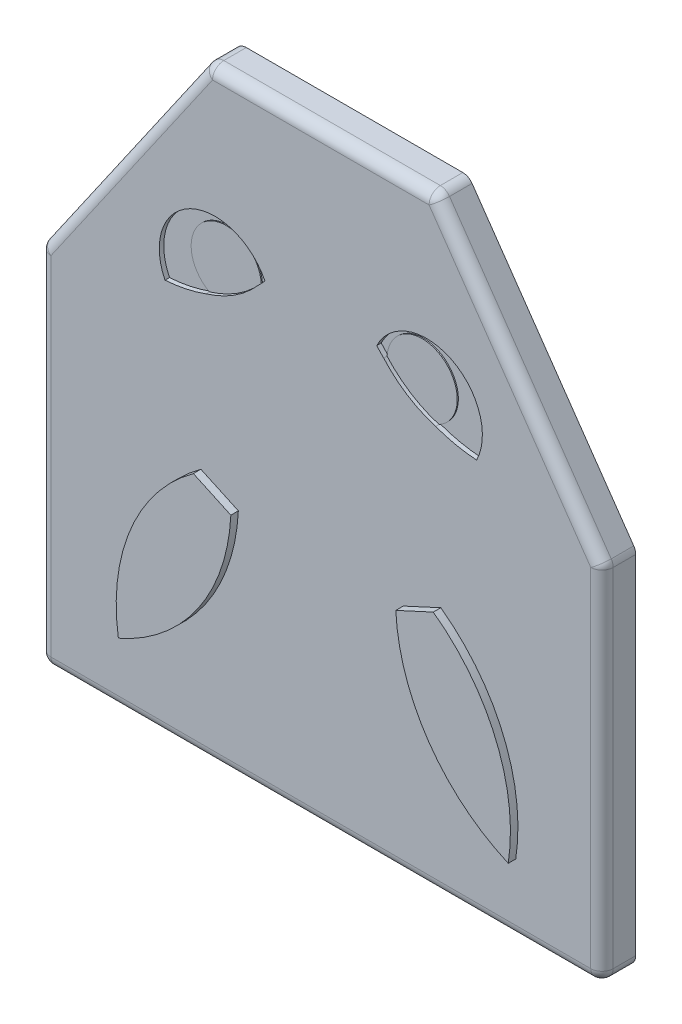
SolidWorks part; units mm, degrees
material "PS HI"
ref_plane "Face" through (0, 0, 0) normal (0, 0, 1) x (1, 0, 0)
ref_plane "Dessus" through (0, 0, 0) normal (0, 1, 0) x (1, 0, 0)
ref_plane "Droite" through (0, 0, 0) normal (1, 0, 0) x (0, 0, -1)
sketch "Esquisse1" plane through (0, 0, 0) normal (0, 0, 1) x (1, 0, 0)
  line L0 (0, 150.787) -> (0, -256.1207) construction
  line L1 (73, -52.6668) -> (-73, -52.6668)
  line L2 (-73, -52.6668) -> (-73, 41.3332)
  line L3 (-73, 41.3332) -> (-29.4, 104.1823)
  line L4 (-29.4, 104.1823) -> (29.4, 104.1823)
  line L5 (73, -52.6668) -> (73, 41.3332)
  line L6 (73, 41.3332) -> (29.4, 104.1823)
  line L7 (-75, 41.959) -> (-30.4467, 106.1823)
  line L8 (-30.4467, 106.1823) -> (30.4467, 106.1823)
  line L9 (75, 41.959) -> (30.4467, 106.1823)
  line L10 (75, -54.6668) -> (75, 41.959)
  line L11 (75, -54.6668) -> (-75, -54.6668)
  line L12 (-75, -54.6668) -> (-75, 41.959)
  point P9 (0, -52.6668)
  point P11 (0, 104.1823)
  dimension "D1" = 73
  dimension "D2" = 94
  dimension "D3" = 34.75
  dimension "D4" = 29.4
  dimension "D5" = 2
extrude "Boss.-Extru.1" add sketch "Esquisse1" against normal blind 9
sketch "Esquisse2" plane through (0, 0, 0) normal (0, 0, 1) x (1, 0, 0)
  line L0 (-73, 41.3332) -> (-29.4, 104.1823)
  line L1 (-29.4, 104.1823) -> (29.4, 104.1823)
  line L2 (29.4, 104.1823) -> (73, 41.3332)
  line L3 (73, 41.3332) -> (73, -52.6668)
  line L4 (73, -52.6668) -> (-73, -52.6668)
  line L5 (-73, -52.6668) -> (-73, 41.3332)
extrude "Boss.-Extru.2" add sketch "Esquisse2" against normal blind 2
fillet "Congé1" radius 3 6 edges at (73, -52.6668, -5.5) (73, 41.3332, -5.5) (29.4, 104.1823, -5.5) (-29.4, 104.1823, -5.5) (-73, 41.3332, -5.5) (-73, -52.6668, -5.5)
fillet "Congé2" radius 3 12 edges at (75, -6.3539, 0) (52.7233, 74.0707, 0) (0, 106.1823, 0) (-52.7233, 74.0707, 0) (-75, -6.3539, 0) (0, -54.6668, 0) (-75, -54.6668, -4.5) (75, -54.6668, -4.5) (75, 41.959, -4.5) (30.4467, 106.1823, -4.5) (-30.4467, 106.1823, -4.5) (-75, 41.959, -4.5)
sketch "Esquisse3" plane through (0, 0, 0) normal (0, 0, 1) x (1, 0, 0)
  line L0 (0, -80.0103) -> (0, 129.0425) construction
  arc A0 (-14.9139, 63.7443) -> (-41.5599, 50.597) centre (-44.0253, 89.1695) cw
  arc A1 (-41.5599, 50.597) -> (-14.9139, 63.7443) centre (-28.2369, 57.1706) cw
  arc A2 (-16.7752, 61.7587) -> (-30.6326, 52.9128) centre (-26.122, 61.1238) ccw
  arc A3 (16.7752, 61.7587) -> (30.6326, 52.9128) centre (26.122, 61.1238) cw
  arc A4 (41.5599, 50.597) -> (14.9139, 63.7443) centre (28.2369, 57.1706) ccw
  arc A5 (14.9139, 63.7443) -> (41.5599, 50.597) centre (44.0253, 89.1695) ccw
extrude "Enlèv. mat.-Extru.2" cut sketch "Esquisse3" against normal blind 1.2 contours A4 A5 A3 | A2 A0 A1
sketch "Esquisse7" plane through (0, 0, 0) normal (0, 0, 1) x (1, 0, 0)
  arc A0 (-30.6326, 52.9128) -> (-16.7752, 61.7587) centre (-26.122, 61.1238) cw
  arc A1 (-16.7752, 61.7587) -> (-30.6326, 52.9128) centre (-39.2283, 81.655) cw
  arc A2 (30.6326, 52.9128) -> (16.7752, 61.7587) centre (26.1239, 61.1267) ccw
  arc A3 (30.6326, 52.9128) -> (16.7752, 61.7587) centre (39.2283, 81.655) cw
  dimension "D1" = 30
  dimension "D2" = 30
  dimension "D3" = 9.37
  dimension "D4" = 9.3684
extrude "Enlèv. mat.-Extru.3" cut sketch "Esquisse7" against normal blind 0.9
sketch "Esquisse8" plane through (0, 0, 0) normal (0, 0, 1) x (1, 0, 0)
  line L0 (0, -111.8536) -> (0, 181.9163) construction
  line L1 (-22, 7.0974) -> (-32, 11.7051)
  line L2 (-72, 41.0203) -> (-72, -51.6668) construction
  line L3 (22, 7.0974) -> (32, 11.7051)
  arc A0 (-22, 7.0974) -> (-52, -36.3341) centre (-71.9414, 9.5172) cw
  arc A1 (-52, -36.3341) -> (-32, 11.7051) centre (-2.5824, -28.7251) cw
  arc A2 (22, 7.0974) -> (52, -36.3341) centre (71.9414, 9.5172) ccw
  arc A3 (52, -36.3341) -> (32, 11.7051) centre (2.5824, -28.7251) ccw
  dimension "D1" = 50
  dimension "D2" = 50
  dimension "D3" = 52
  dimension "D4" = 20
  dimension "D5" = 40
  dimension "D6" = 50
extrude "Boss.-Extru.3" add sketch "Esquisse8" along normal blind 2
sketch "Esquisse9" plane through (0, 0, -9) normal (0, 0, -1) x (-1, 0, 0)
  line L0 (0, -94.0673) -> (0, 202.1869) construction
  line L1 (-30, -54.6668) -> (30, -54.6668)
  line L2 (72, -54.6668) -> (-72, -54.6668) construction
  line L3 (30, -54.6668) -> (30, -52.6668)
  line L4 (70, -52.6668) -> (-70, -52.6668) construction
  line L5 (30, -52.6668) -> (-30, -52.6668)
  line L6 (-30, -54.6668) -> (-30, -52.6668)
  point P12 (0, -54.6668)
  point P13 (0, -52.6668)
  dimension "D1" = 30
extrude "Boss.-Extru.4" add sketch "Esquisse9" along normal blind 34
sketch "Esquisse10" plane through (0, -52.6668, 0) normal (0, 1, 0) x (1, 0, 0)
  line L0 (0, -10.6573) -> (0, 70.3206) construction
  line L1 (25, 41) -> (-25, 41)
  line L2 (-30, 43) -> (30, 43) construction
  arc A0 (25, 41) -> (-25, 41) centre (0, 41) cw
  dimension "D2" = 25
  dimension "D1" = 50
  dimension "D3" = 2
extrude "Boss.-Extru.5" add sketch "Esquisse10" along normal blind 3
